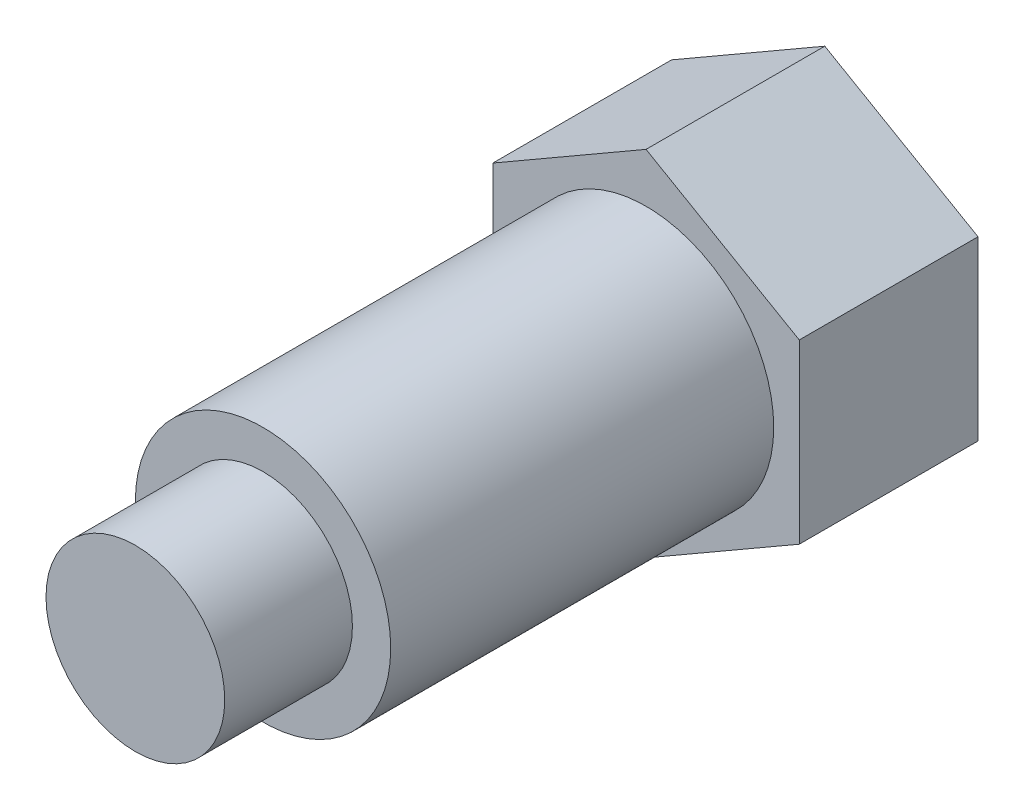
SolidWorks part; units mm, degrees
ref_plane "Спереди" through (0, 0, 0) normal (0, 0, 1) x (1, 0, 0)
ref_plane "Сверху" through (0, 0, 0) normal (0, 1, 0) x (1, 0, 0)
ref_plane "Справа" through (0, 0, 0) normal (1, 0, 0) x (0, 0, -1)
sketch "Sketch1" plane through (0, 0, 0) normal (0, 1, 0) x (1, 0, 0)
  line L0 (0, 0) -> (0, -20)
  line L1 (0, -20) -> (3.5, -20)
  line L2 (3.5, -20) -> (3.5, -15)
  line L3 (3.5, -15) -> (5, -15)
  line L4 (5, -15) -> (5, 0)
  line L5 (0, 0) -> (5, 0)
  line L6 (0, 1.1873) -> (0, -43.9301) construction
  dimension "D" = 10
  dimension "L" = 20
  dimension "DP" = 7
  dimension "Z2" = 5
revolve "Base-Revolve" add sketch "Sketch1"
cosmetic thread "Cosmetic Thread1"
extrude "Boss-Extrude1" add sketch "Sketch2" along normal blind 7
sketch "Sketch2" plane through (0, 0, 0) normal (0, 0, -1) x (-1, 0, 0)
  line L1 (6, -3.4641) -> (6, 3.4641)
  line L2 (6, 3.4641) -> (0, 6.9282)
  line L3 (0, 6.9282) -> (-6, 3.4641)
  line L4 (-6, 3.4641) -> (-6, -3.4641)
  line L5 (-6, -3.4641) -> (0, -6.9282)
  line L6 (0, -6.9282) -> (6, -3.4641)
  circle A0 centre (0, 0) radius 6 construction
  dimension "S" = 12
